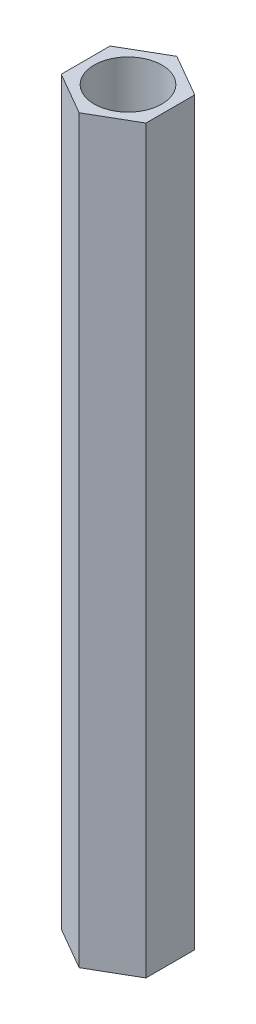
SolidWorks part; units mm, degrees
ref_plane "前视基准面" through (0, 0, 0) normal (0, 0, 1) x (1, 0, 0)
ref_plane "上视基准面" through (0, 0, 0) normal (0, 1, 0) x (1, 0, 0)
ref_plane "右视基准面" through (0, 0, 0) normal (1, 0, 0) x (0, 0, -1)
sketch "草图1" plane through (0, 0, 0) normal (0, 1, 0) x (1, 0, 0)
  line L1 (2.0004, -1.1541) -> (1.9996, 1.1553)
  line L2 (1.9996, 1.1553) -> (-0.0007, 2.3094)
  line L3 (-0.0007, 2.3094) -> (-2.0004, 1.1541)
  line L4 (-2.0004, 1.1541) -> (-1.9996, -1.1553)
  line L5 (-1.9996, -1.1553) -> (0.0007, -2.3094)
  line L6 (0.0007, -2.3094) -> (2.0004, -1.1541)
  circle A0 centre (0, 0) radius 2 construction
  dimension "D1" = 4
extrude "凸台-拉伸1" add sketch "草图1" along normal blind 35
sketch "草图2" plane through (0, 35, 0) normal (0, 1, 0) x (1, 0, 0)
  circle A0 centre (0, 0) radius 1.6
  dimension "D1" = 3.2
extrude "切除-拉伸1" cut sketch "草图2" against normal through all
